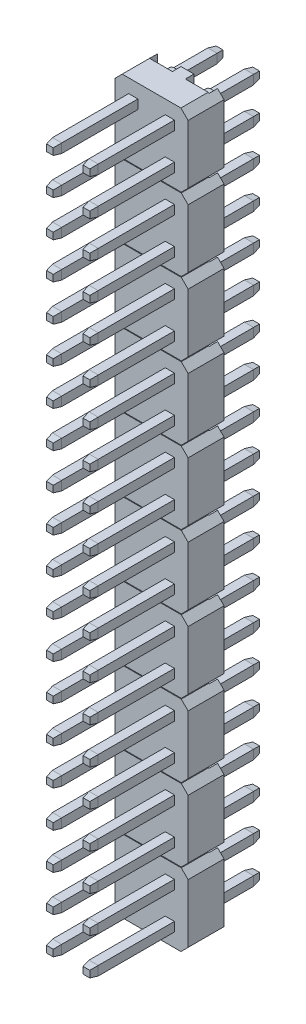
SolidWorks part; units mm, degrees
ref_plane "Płaszczyzna przednia" through (0, 0, 0) normal (0, 0, 1) x (1, 0, 0)
ref_plane "Płaszczyzna górna" through (0, 0, 0) normal (0, 1, 0) x (1, 0, 0)
ref_plane "Płaszczyzna prawa" through (0, 0, 0) normal (1, 0, 0) x (0, 0, -1)
sketch "Sketch1" plane through (0, 0, 0) normal (0, 0, 1) x (1, 0, 0)
  line L1 (1.27, 1.27) -> (-1.27, 1.27) construction
  line L2 (1.27, 1.27) -> (1.27, -1.27) construction
  line L3 (1.27, -1.27) -> (-1.27, -1.27) construction
  line L4 (-1.27, 1.27) -> (-1.27, -1.27) construction
  line L5 (1.27, 1.27) -> (-1.27, -1.27) construction
  line L6 (1.27, -1.27) -> (-1.27, 1.27) construction
  line L7 (-0.95, 0.95) -> (-1.59, 0.95)
  line L8 (-0.95, 0.95) -> (-0.95, 1.59)
  line L9 (-0.95, 1.59) -> (-1.59, 1.59)
  line L10 (-1.59, 0.95) -> (-1.59, 1.59)
  line L11 (-0.95, 0.95) -> (-1.59, 1.59) construction
  line L12 (-0.95, 1.59) -> (-1.59, 0.95) construction
  line L13 (-0.95, -0.95) -> (-1.59, -0.95)
  line L14 (-0.95, -0.95) -> (-0.95, -1.59)
  line L15 (-0.95, -1.59) -> (-1.59, -1.59)
  line L16 (-1.59, -0.95) -> (-1.59, -1.59)
  line L17 (-0.95, -0.95) -> (-1.59, -1.59) construction
  line L18 (-0.95, -1.59) -> (-1.59, -0.95) construction
  line L19 (0.95, 0.95) -> (1.59, 0.95)
  line L20 (0.95, 0.95) -> (0.95, 1.59)
  line L21 (0.95, 1.59) -> (1.59, 1.59)
  line L22 (1.59, 0.95) -> (1.59, 1.59)
  line L23 (0.95, 0.95) -> (1.59, 1.59) construction
  line L24 (0.95, 1.59) -> (1.59, 0.95) construction
  line L25 (0.95, -1.59) -> (1.59, -1.59)
  line L26 (0.95, -1.59) -> (0.95, -0.95)
  line L27 (0.95, -0.95) -> (1.59, -0.95)
  line L28 (1.59, -1.59) -> (1.59, -0.95)
  line L29 (0.95, -1.59) -> (1.59, -0.95) construction
  line L30 (0.95, -0.95) -> (1.59, -1.59) construction
  point P0 (0, 0)
extrude "Boss-Extrude1" add sketch "Sketch1" along normal blind 5.3
sketch "Sketch2" plane through (0, 0, 5.3) normal (0, 0, 1) x (1, 0, 0)
  line L4 (-1.59, -0.95) -> (-1.59, -1.59)
  line L5 (-1.59, -1.59) -> (-0.95, -1.59)
  line L6 (-0.95, -1.59) -> (-0.95, -0.95)
  line L7 (-0.95, -0.95) -> (-1.59, -0.95)
  line L8 (-1.59, -0.95) -> (-1.59, -1.59)
  line L9 (-1.59, -1.59) -> (-0.95, -1.59)
  line L10 (-0.95, -1.59) -> (-0.95, -0.95)
  line L11 (-0.95, -0.95) -> (-1.59, -0.95)
  line L12 (-1.59, 1.59) -> (-1.59, 0.95)
  line L13 (-1.59, 0.95) -> (-0.95, 0.95)
  line L14 (-0.95, 0.95) -> (-0.95, 1.59)
  line L15 (-0.95, 1.59) -> (-1.59, 1.59)
  line L16 (-1.59, 1.59) -> (-1.59, 0.95)
  line L17 (-1.59, 0.95) -> (-0.95, 0.95)
  line L18 (-0.95, 0.95) -> (-0.95, 1.59)
  line L19 (-0.95, 1.59) -> (-1.59, 1.59)
  line L20 (1.59, -1.59) -> (1.59, -0.95)
  line L21 (1.59, -0.95) -> (0.95, -0.95)
  line L22 (0.95, -0.95) -> (0.95, -1.59)
  line L23 (0.95, -1.59) -> (1.59, -1.59)
  line L24 (1.59, -1.59) -> (1.59, -0.95)
  line L25 (1.59, -0.95) -> (0.95, -0.95)
  line L26 (0.95, -0.95) -> (0.95, -1.59)
  line L27 (0.95, -1.59) -> (1.59, -1.59)
  line L28 (1.59, 0.95) -> (1.59, 1.59)
  line L29 (1.59, 1.59) -> (0.95, 1.59)
  line L30 (0.95, 1.59) -> (0.95, 0.95)
  line L31 (0.95, 0.95) -> (1.59, 0.95)
  line L32 (1.59, 0.95) -> (1.59, 1.59)
  line L33 (1.59, 1.59) -> (0.95, 1.59)
  line L34 (0.95, 1.59) -> (0.95, 0.95)
  line L35 (0.95, 0.95) -> (1.59, 0.95)
  dimension "D1" = 0
  dimension "D2" = 0
  dimension "D3" = 0
  dimension "D4" = 0
extrude "Boss-Extrude2" add sketch "Sketch2" along normal blind 0.5 draft 10
sketch "Sketch3" plane through (0, 0, 0) normal (0, 0, 1) x (1, 0, 0)
  line L1 (-2.04, 2.54) -> (2.04, 2.54)
  line L2 (-2.54, 2.04) -> (-2.54, -2.04)
  line L3 (-2.04, -2.54) -> (2.04, -2.54)
  line L4 (2.54, 2.04) -> (2.54, -2.04)
  line L5 (-2.54, 2.54) -> (2.54, -2.54) construction
  line L6 (-2.54, -2.54) -> (2.54, 2.54) construction
  line L24 (-2.54, -2.04) -> (-2.04, -2.54)
  line L25 (2.04, -2.54) -> (2.54, -2.04)
  line L26 (2.04, 2.54) -> (2.54, 2.04)
  line L27 (-2.54, 2.04) -> (-2.04, 2.54)
  point P0 (0, 0)
extrude "Boss-Extrude3" add sketch "Sketch3" against normal blind 2.5 separate body
sketch "Sketch5" plane through (0, 0, -2.5) normal (0, 0, -1) x (-1, 0, 0)
  line L0 (-0.45, -2.54) -> (-0.45, 2.54)
  line L1 (2.04, -2.54) -> (-2.04, -2.54) construction
  line L2 (-2.04, 2.54) -> (2.04, 2.54) construction
  line L3 (-2.09, -2.54) -> (-2.09, 2.54)
  line L4 (-2.54, -2.04) -> (-2.54, 2.04) construction
  line L5 (-0.95, -0.95) -> (-0.95, -1.59) construction
  line L7 (0, -2.54) -> (0, -3.101) construction
  line L8 (2.09, -2.54) -> (2.09, 2.54)
  line L9 (0.45, -2.54) -> (0.45, 2.54)
  line L10 (2.09, -2.54) -> (0.45, -2.54)
  line L11 (-0.45, -2.54) -> (-2.09, -2.54)
  line L12 (2.09, 2.54) -> (0.45, 2.54)
  line L13 (-0.45, 2.54) -> (-2.09, 2.54)
  dimension "D1" = 0.45
  dimension "D2" = 0.5
extrude "Cut-Extrude1" cut sketch "Sketch5" against normal blind 0.6
sketch "Sketch6" plane through (0, 0, 0) normal (0, 0, 1) x (1, 0, 0)
  line L0 (2.54, 0) -> (-2.54, 0) construction
  line L1 (2.54, -2.04) -> (2.54, 2.04) construction
  line L2 (-2.54, 2.04) -> (-2.54, -2.04) construction
  line L3 (-2.54, 0.05) -> (-2.54, -0.05)
  line L4 (-2.54, 0.05) -> (2.54, 0.05)
  line L5 (2.54, 0.05) -> (2.54, -0.05)
  line L6 (2.54, -0.05) -> (-2.54, -0.05)
  dimension "D1" = 0.1
sketch "Sketch8" plane through (0, 0, -1.9) normal (0, 0, -1) x (-1, 0, 0)
  line L0 (1.59, -1.59) -> (0.95, -1.59)
  line L1 (0.95, -1.59) -> (0.95, -0.95)
  line L2 (0.95, -0.95) -> (1.59, -0.95)
  line L3 (1.59, -0.95) -> (1.59, -1.59)
  line L12 (0.95, 1.59) -> (1.59, 1.59) construction
  line L13 (0.95, 0.95) -> (0.95, 1.59) construction
  line L14 (1.59, 1.59) -> (1.59, 0.95) construction
  line L15 (1.59, 0.95) -> (0.95, 0.95) construction
  line L16 (-0.95, 0.95) -> (-1.59, 0.95) construction
  line L17 (-0.95, 1.59) -> (-0.95, 0.95) construction
  line L18 (-1.59, 1.59) -> (-0.95, 1.59) construction
  line L19 (-1.59, 0.95) -> (-1.59, 1.59) construction
  line L20 (-1.59, -0.95) -> (-0.95, -0.95) construction
  line L21 (-1.59, -1.59) -> (-1.59, -0.95) construction
  line L22 (-0.95, -0.95) -> (-0.95, -1.59) construction
  line L23 (-0.95, -1.59) -> (-1.59, -1.59) construction
  line L32 (0.95, 1.59) -> (1.59, 1.59)
  line L33 (0.95, 0.95) -> (0.95, 1.59)
  line L34 (1.59, 1.59) -> (1.59, 0.95)
  line L35 (1.59, 0.95) -> (0.95, 0.95)
  line L36 (-0.95, 0.95) -> (-1.59, 0.95)
  line L37 (-0.95, 1.59) -> (-0.95, 0.95)
  line L38 (-1.59, 1.59) -> (-0.95, 1.59)
  line L39 (-1.59, 0.95) -> (-1.59, 1.59)
  line L40 (-1.59, -0.95) -> (-0.95, -0.95)
  line L41 (-1.59, -1.59) -> (-1.59, -0.95)
  line L42 (-0.95, -0.95) -> (-0.95, -1.59)
  line L43 (-0.95, -1.59) -> (-1.59, -1.59)
extrude "Boss-Extrude4" add sketch "Sketch8" along normal blind 3.6 separate body
sketch "Sketch9" plane through (0, 0, -5.5) normal (0, 0, -1) x (-1, 0, 0)
  line L4 (0.95, 1.59) -> (0.95, 0.95)
  line L5 (0.95, 0.95) -> (1.59, 0.95)
  line L6 (1.59, 0.95) -> (1.59, 1.59)
  line L7 (1.59, 1.59) -> (0.95, 1.59)
  line L8 (0.95, 1.59) -> (0.95, 0.95)
  line L9 (0.95, 0.95) -> (1.59, 0.95)
  line L10 (1.59, 0.95) -> (1.59, 1.59)
  line L11 (1.59, 1.59) -> (0.95, 1.59)
  line L12 (1.59, -1.59) -> (1.59, -0.95)
  line L13 (1.59, -0.95) -> (0.95, -0.95)
  line L14 (0.95, -0.95) -> (0.95, -1.59)
  line L15 (0.95, -1.59) -> (1.59, -1.59)
  line L16 (1.59, -1.59) -> (1.59, -0.95)
  line L17 (1.59, -0.95) -> (0.95, -0.95)
  line L18 (0.95, -0.95) -> (0.95, -1.59)
  line L19 (0.95, -1.59) -> (1.59, -1.59)
  line L20 (-1.59, -0.95) -> (-1.59, -1.59)
  line L21 (-1.59, -1.59) -> (-0.95, -1.59)
  line L22 (-0.95, -1.59) -> (-0.95, -0.95)
  line L23 (-0.95, -0.95) -> (-1.59, -0.95)
  line L24 (-1.59, -0.95) -> (-1.59, -1.59)
  line L25 (-1.59, -1.59) -> (-0.95, -1.59)
  line L26 (-0.95, -1.59) -> (-0.95, -0.95)
  line L27 (-0.95, -0.95) -> (-1.59, -0.95)
  line L28 (-0.95, 0.95) -> (-0.95, 1.59)
  line L29 (-0.95, 1.59) -> (-1.59, 1.59)
  line L30 (-1.59, 1.59) -> (-1.59, 0.95)
  line L31 (-1.59, 0.95) -> (-0.95, 0.95)
  line L32 (-0.95, 0.95) -> (-0.95, 1.59)
  line L33 (-0.95, 1.59) -> (-1.59, 1.59)
  line L34 (-1.59, 1.59) -> (-1.59, 0.95)
  line L35 (-1.59, 0.95) -> (-0.95, 0.95)
  dimension "D1" = 0
  dimension "D2" = 0
  dimension "D3" = 0
  dimension "D4" = 0
extrude "Boss-Extrude5" add sketch "Sketch9" along normal blind 0.5 draft 10
sketch "Sketch10" plane through (0, 0, -1.9) normal (0, 0, -1) x (-1, 0, 0)
  line L0 (-1.27, 1.0382) -> (-1.27, 1.5018) construction
  line L1 (-1.5018, 1.0382) -> (-1.0382, 1.0382) construction
  line L2 (-1.0382, 1.5018) -> (-1.5018, 1.5018) construction
  line L3 (1.27, 1.5018) -> (1.27, 1.0382) construction
  line L4 (1.5018, 1.5018) -> (1.0382, 1.5018) construction
  line L5 (1.0382, 1.0382) -> (1.5018, 1.0382) construction
  circle A0 centre (-1.27, 1.27) radius 0.56
  circle A1 centre (1.27, 1.27) radius 0.56
extrude "Boss-Extrude6" add sketch "Sketch10" along normal blind 1 separate body
pattern_linear "Szyk liniowy1" count 10 spacing 5.08 along (0, -1, 0) of bodies 110 105 107 108 106 119 120 122 121
sketch "Szkic1" plane through (0, 0, 0) normal (0, 0, 1) x (1, 0, 0)
  line L0 (0, -2.54) -> (3.1531, -2.54) construction
  line L1 (2.04, -2.54) -> (-2.04, -2.54) construction
  line L2 (-2.3421, -7.645) -> (2.3421, -7.645)
  line L3 (-2.3421, -2.565) -> (2.3421, -2.565)
  line L4 (-2.3421, -2.565) -> (-2.3421, -2.515)
  line L5 (-2.3421, -2.515) -> (2.3421, -2.515)
  line L6 (2.3421, -2.565) -> (2.3421, -2.515)
  line L7 (-2.3421, -2.565) -> (2.3421, -2.515) construction
  line L8 (-2.3421, -2.515) -> (2.3421, -2.565) construction
  line L9 (-2.3421, -7.595) -> (2.3421, -7.595)
  line L10 (2.3421, -7.645) -> (2.3421, -7.595)
  line L11 (-2.3421, -7.645) -> (-2.3421, -7.595)
  line L12 (-2.3421, -12.725) -> (2.3421, -12.725)
  line L13 (-2.3421, -12.675) -> (2.3421, -12.675)
  line L14 (2.3421, -12.725) -> (2.3421, -12.675)
  line L15 (-2.3421, -12.725) -> (-2.3421, -12.675)
  line L16 (-2.3421, -17.805) -> (2.3421, -17.805)
  line L17 (-2.3421, -17.755) -> (2.3421, -17.755)
  line L18 (2.3421, -17.805) -> (2.3421, -17.755)
  line L19 (-2.3421, -17.805) -> (-2.3421, -17.755)
  line L20 (-2.3421, -22.885) -> (2.3421, -22.885)
  line L21 (-2.3421, -22.835) -> (2.3421, -22.835)
  line L22 (2.3421, -22.885) -> (2.3421, -22.835)
  line L23 (-2.3421, -22.885) -> (-2.3421, -22.835)
  line L24 (-2.3421, -27.965) -> (2.3421, -27.965)
  line L25 (-2.3421, -27.915) -> (2.3421, -27.915)
  line L26 (2.3421, -27.965) -> (2.3421, -27.915)
  line L27 (-2.3421, -27.965) -> (-2.3421, -27.915)
  line L28 (-2.3421, -33.045) -> (2.3421, -33.045)
  line L29 (-2.3421, -32.995) -> (2.3421, -32.995)
  line L30 (2.3421, -33.045) -> (2.3421, -32.995)
  line L31 (-2.3421, -33.045) -> (-2.3421, -32.995)
  line L32 (-2.3421, -38.125) -> (2.3421, -38.125)
  line L33 (-2.3421, -38.075) -> (2.3421, -38.075)
  line L34 (2.3421, -38.125) -> (2.3421, -38.075)
  line L35 (-2.3421, -38.125) -> (-2.3421, -38.075)
  line L36 (-2.3421, -43.205) -> (2.3421, -43.205)
  line L37 (-2.3421, -43.155) -> (2.3421, -43.155)
  line L38 (2.3421, -43.205) -> (2.3421, -43.155)
  line L39 (-2.3421, -43.205) -> (-2.3421, -43.155)
  dimension "D1" = 0.05
  dimension "D2" = 9
extrude "Wytnij-wyciągnięcie1" cut sketch "Szkic1" against normal through all
